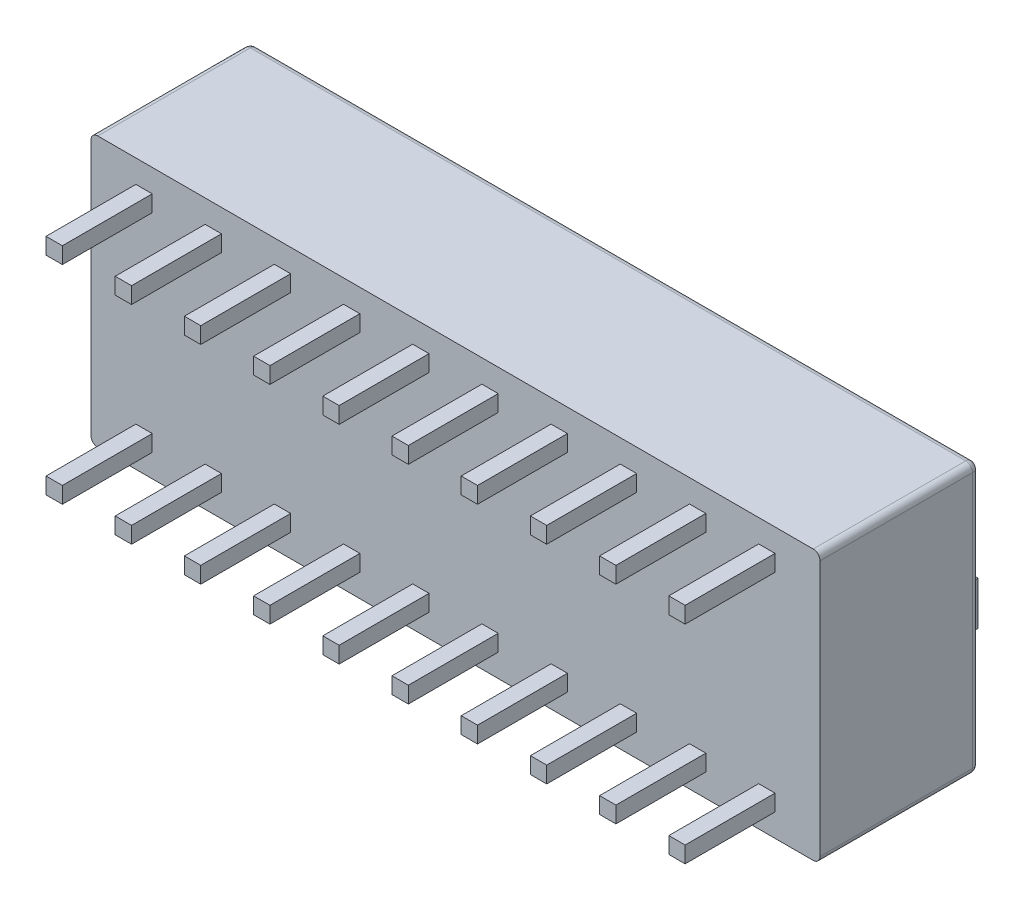
SolidWorks part; units mm, degrees
ref_plane "Ön Düzlem" through (0, 0, 0) normal (0, 0, 1) x (1, 0, 0)
ref_plane "Üst Düzlem" through (0, 0, 0) normal (0, 1, 0) x (1, 0, 0)
ref_plane "Sağ Düzlem" through (0, 0, 0) normal (1, 0, 0) x (0, 0, -1)
sketch "Çizim1" plane through (0, 0, 0) normal (0, 0, 1) x (1, 0, 0)
  line L1 (-13.38, 4.95) -> (13.38, 4.95)
  line L2 (-13.38, 4.95) -> (-13.38, -4.95)
  line L3 (-13.38, -4.95) -> (13.38, -4.95)
  line L4 (13.38, 4.95) -> (13.38, -4.95)
  line L5 (-13.38, 4.95) -> (13.38, -4.95) construction
  line L6 (-13.38, -4.95) -> (13.38, 4.95) construction
  point P0 (0, 0)
extrude "Yükseklik-Ekstrüzyon1" add sketch "Çizim1" along normal blind 5.85
sketch "Çizim2" plane through (0, 0, 0) normal (0, 0, -1) x (-1, 0, 0)
  line L1 (-12.13, 1.6) -> (-10.73, 1.6)
  line L11 (-12.13, 1.6) -> (-12.13, -1.6)
  line L12 (-12.13, -1.6) -> (-10.73, -1.6)
  line L13 (-10.73, 1.6) -> (-10.73, -1.6)
  line L14 (-12.13, 1.6) -> (-10.73, -1.6) construction
  line L15 (-12.13, -1.6) -> (-10.73, 1.6) construction
  line L16 (-9.59, 1.6) -> (-8.19, 1.6)
  line L17 (-9.59, 1.6) -> (-9.59, -1.6)
  line L18 (-9.59, -1.6) -> (-8.19, -1.6)
  line L19 (-8.19, 1.6) -> (-8.19, -1.6)
  line L20 (-9.59, 1.6) -> (-8.19, -1.6) construction
  line L21 (-9.59, -1.6) -> (-8.19, 1.6) construction
  line L22 (-7.05, 1.6) -> (-5.65, 1.6)
  line L23 (-7.05, 1.6) -> (-7.05, -1.6)
  line L24 (-7.05, -1.6) -> (-5.65, -1.6)
  line L25 (-5.65, 1.6) -> (-5.65, -1.6)
  line L26 (-7.05, 1.6) -> (-5.65, -1.6) construction
  line L27 (-7.05, -1.6) -> (-5.65, 1.6) construction
  line L28 (-4.51, 1.6) -> (-3.11, 1.6)
  line L29 (-4.51, 1.6) -> (-4.51, -1.6)
  line L30 (-4.51, -1.6) -> (-3.11, -1.6)
  line L31 (-3.11, 1.6) -> (-3.11, -1.6)
  line L32 (-4.51, 1.6) -> (-3.11, -1.6) construction
  line L33 (-4.51, -1.6) -> (-3.11, 1.6) construction
  line L34 (-1.97, 1.6) -> (-0.57, 1.6)
  line L35 (-1.97, 1.6) -> (-1.97, -1.6)
  line L36 (-1.97, -1.6) -> (-0.57, -1.6)
  line L37 (-0.57, 1.6) -> (-0.57, -1.6)
  line L38 (-1.97, 1.6) -> (-0.57, -1.6) construction
  line L39 (-1.97, -1.6) -> (-0.57, 1.6) construction
  line L40 (0.57, 1.6) -> (1.97, 1.6)
  line L41 (0.57, 1.6) -> (0.57, -1.6)
  line L42 (0.57, -1.6) -> (1.97, -1.6)
  line L43 (1.97, 1.6) -> (1.97, -1.6)
  line L44 (0.57, 1.6) -> (1.97, -1.6) construction
  line L45 (0.57, -1.6) -> (1.97, 1.6) construction
  line L46 (3.11, 1.6) -> (4.51, 1.6)
  line L47 (3.11, 1.6) -> (3.11, -1.6)
  line L48 (3.11, -1.6) -> (4.51, -1.6)
  line L49 (4.51, 1.6) -> (4.51, -1.6)
  line L50 (3.11, 1.6) -> (4.51, -1.6) construction
  line L51 (3.11, -1.6) -> (4.51, 1.6) construction
  line L52 (5.65, 1.6) -> (7.05, 1.6)
  line L53 (5.65, 1.6) -> (5.65, -1.6)
  line L54 (5.65, -1.6) -> (7.05, -1.6)
  line L55 (7.05, 1.6) -> (7.05, -1.6)
  line L56 (5.65, 1.6) -> (7.05, -1.6) construction
  line L57 (5.65, -1.6) -> (7.05, 1.6) construction
  line L58 (8.19, 1.6) -> (9.59, 1.6)
  line L59 (8.19, 1.6) -> (8.19, -1.6)
  line L60 (8.19, -1.6) -> (9.59, -1.6)
  line L61 (9.59, 1.6) -> (9.59, -1.6)
  line L62 (8.19, 1.6) -> (9.59, -1.6) construction
  line L63 (8.19, -1.6) -> (9.59, 1.6) construction
  line L64 (10.73, 1.6) -> (12.13, 1.6)
  line L65 (10.73, 1.6) -> (10.73, -1.6)
  line L66 (10.73, -1.6) -> (12.13, -1.6)
  line L67 (12.13, 1.6) -> (12.13, -1.6)
  line L68 (10.73, 1.6) -> (12.13, -1.6) construction
  line L69 (10.73, -1.6) -> (12.13, 1.6) construction
extrude "Kes-Ekstrüzyon1" cut sketch "Çizim2" against normal blind 1
sketch "Çizim3" plane through (0, 0, 1) normal (0, 0, -1) x (-1, 0, 0)
  line L0 (-10.73, -1.6) -> (-10.73, 1.6) construction
  line L1 (-12.13, -1.6) -> (-10.73, -1.6)
  line L2 (-12.13, -1.6) -> (-12.13, 0)
  line L3 (-12.13, 0) -> (-10.73, 0)
  line L4 (-10.73, -1.6) -> (-10.73, 0)
  line L5 (-9.59, 1.6) -> (-9.59, -1.6) construction
  line L6 (-9.59, 0) -> (-8.19, 0)
  line L7 (-9.59, 0) -> (-9.59, -1.6)
  line L8 (-9.59, -1.6) -> (-8.19, -1.6)
  line L9 (-8.19, 0) -> (-8.19, -1.6)
  line L10 (-7.05, -1.6) -> (-5.65, -1.6) construction
  line L11 (-7.05, -1.6) -> (-5.65, -1.6)
  line L12 (-7.05, -1.6) -> (-7.05, 0)
  line L13 (-7.05, 0) -> (-5.65, 0)
  line L14 (-5.65, -1.6) -> (-5.65, 0)
  line L15 (-7.05, -1.6) -> (-5.65, -1.6) construction
  line L16 (-5.65, -1.6) -> (-5.65, 1.6) construction
  line L17 (-4.51, 1.6) -> (-4.51, -1.6) construction
  line L18 (-4.51, 0) -> (-3.11, 0)
  line L19 (-4.51, 0) -> (-4.51, -1.6)
  line L20 (-4.51, -1.6) -> (-3.11, -1.6)
  line L21 (-3.11, 0) -> (-3.11, -1.6)
  line L22 (-0.57, -1.6) -> (-0.57, 1.6) construction
  line L23 (-1.97, -1.6) -> (-0.57, -1.6)
  line L24 (-1.97, -1.6) -> (-1.97, 0)
  line L25 (-1.97, 0) -> (-0.57, 0)
  line L26 (-0.57, -1.6) -> (-0.57, 0)
  line L27 (0.57, 1.6) -> (0.57, -1.6) construction
  line L28 (0.57, 0) -> (1.97, 0)
  line L29 (0.57, 0) -> (0.57, -1.6)
  line L30 (0.57, -1.6) -> (1.97, -1.6)
  line L31 (1.97, 0) -> (1.97, -1.6)
  line L32 (4.51, -1.6) -> (4.51, 1.6) construction
  line L33 (3.11, -1.6) -> (4.51, -1.6)
  line L34 (3.11, -1.6) -> (3.11, 0)
  line L35 (3.11, 0) -> (4.51, 0)
  line L36 (4.51, -1.6) -> (4.51, 0)
  line L37 (5.65, 1.6) -> (5.65, -1.6) construction
  line L38 (5.65, 0) -> (7.05, 0)
  line L39 (5.65, 0) -> (5.65, -1.6)
  line L40 (5.65, -1.6) -> (7.05, -1.6)
  line L41 (7.05, 0) -> (7.05, -1.6)
  line L42 (9.59, -1.6) -> (9.59, 1.6) construction
  line L43 (8.19, -1.6) -> (9.59, -1.6)
  line L44 (8.19, -1.6) -> (8.19, 0)
  line L45 (8.19, 0) -> (9.59, 0)
  line L46 (9.59, -1.6) -> (9.59, 0)
  line L47 (10.73, 1.6) -> (10.73, -1.6) construction
  line L48 (10.73, 0) -> (12.13, 0)
  line L49 (10.73, 0) -> (10.73, -1.6)
  line L50 (10.73, -1.6) -> (12.13, -1.6)
  line L51 (12.13, 0) -> (12.13, -1.6)
extrude "Yükseklik-Ekstrüzyon2" add sketch "Çizim3" along normal blind 2.2 separate body
sketch "Çizim4" plane through (0, 0, 1) normal (0, 0, -1) x (-1, 0, 0)
  line L0 (-10.73, -1.6) -> (-10.73, 1.6) construction
  line L1 (-12.13, 1.6) -> (-10.73, 1.6)
  line L2 (-12.13, 1.6) -> (-12.13, 0)
  line L3 (-12.13, 0) -> (-10.73, 0)
  line L4 (-10.73, 1.6) -> (-10.73, 0)
  line L5 (-5.65, -1.6) -> (-5.65, 1.6) construction
  line L6 (-9.59, 0) -> (-8.19, 0)
  line L7 (-9.59, 0) -> (-9.59, 1.6)
  line L8 (-9.59, 1.6) -> (-8.19, 1.6)
  line L9 (-8.19, 0) -> (-8.19, 1.6)
  line L10 (-7.05, 1.6) -> (-5.65, 1.6)
  line L11 (-7.05, 1.6) -> (-7.05, 0)
  line L12 (-7.05, 0) -> (-5.65, 0)
  line L13 (-5.65, 1.6) -> (-5.65, 0)
  line L14 (-0.57, -1.6) -> (-0.57, 1.6) construction
  line L15 (-4.51, 0) -> (-3.11, 0)
  line L16 (-4.51, 0) -> (-4.51, 1.6)
  line L17 (-4.51, 1.6) -> (-3.11, 1.6)
  line L18 (-3.11, 0) -> (-3.11, 1.6)
  line L19 (-1.97, 1.6) -> (-0.57, 1.6)
  line L20 (-1.97, 1.6) -> (-1.97, 0)
  line L21 (-1.97, 0) -> (-0.57, 0)
  line L22 (-0.57, 1.6) -> (-0.57, 0)
  line L23 (0.57, 1.6) -> (0.57, -1.6) construction
  line L24 (0.57, 0) -> (1.97, 0)
  line L25 (0.57, 0) -> (0.57, 1.6)
  line L26 (0.57, 1.6) -> (1.97, 1.6)
  line L27 (1.97, 0) -> (1.97, 1.6)
  line L28 (5.65, 1.6) -> (5.65, -1.6) construction
  line L29 (3.11, 1.6) -> (4.51, 1.6)
  line L30 (3.11, 1.6) -> (3.11, 0)
  line L31 (3.11, 0) -> (4.51, 0)
  line L32 (4.51, 1.6) -> (4.51, 0)
  line L33 (5.65, 0) -> (7.05, 0)
  line L34 (5.65, 0) -> (5.65, 1.6)
  line L35 (5.65, 1.6) -> (7.05, 1.6)
  line L36 (7.05, 0) -> (7.05, 1.6)
  line L37 (10.73, 1.6) -> (10.73, -1.6) construction
  line L38 (8.19, 1.6) -> (9.59, 1.6)
  line L39 (8.19, 1.6) -> (8.19, 0)
  line L40 (8.19, 0) -> (9.59, 0)
  line L41 (9.59, 1.6) -> (9.59, 0)
  line L42 (10.73, 0) -> (12.13, 0)
  line L43 (10.73, 0) -> (10.73, 1.6)
  line L44 (10.73, 1.6) -> (12.13, 1.6)
  line L45 (12.13, 0) -> (12.13, 1.6)
extrude "Yükseklik-Ekstrüzyon3" add sketch "Çizim4" along normal blind 0.9 separate body
fillet "Radyus1" radius 0.25 8 edges at (13.38, -4.95, 2.925) (13.38, 4.95, 2.925) (13.38, 0, 0) (-13.38, -4.95, 2.925) (-13.38, 4.95, 2.925) (0, -4.95, 0) (-13.38, 0, 0) (0, 4.95, 0)
sketch "Çizim5" plane through (0, 0, 5.85) normal (0, 0, 1) x (1, 0, 0)
  line L21 (11.73, -4.11) -> (11.13, -4.11)
  line L22 (11.73, -4.11) -> (11.73, -3.51)
  line L23 (11.73, -3.51) -> (11.13, -3.51)
  line L24 (11.13, -4.11) -> (11.13, -3.51)
  line L25 (11.73, -4.11) -> (11.13, -3.51) construction
  line L26 (11.73, -3.51) -> (11.13, -4.11) construction
  line L27 (9.19, -4.11) -> (8.59, -4.11)
  line L28 (9.19, -4.11) -> (9.19, -3.51)
  line L29 (9.19, -3.51) -> (8.59, -3.51)
  line L30 (8.59, -4.11) -> (8.59, -3.51)
  line L31 (9.19, -4.11) -> (8.59, -3.51) construction
  line L32 (9.19, -3.51) -> (8.59, -4.11) construction
  line L33 (6.65, -4.11) -> (6.05, -4.11)
  line L34 (6.65, -4.11) -> (6.65, -3.51)
  line L35 (6.65, -3.51) -> (6.05, -3.51)
  line L36 (6.05, -4.11) -> (6.05, -3.51)
  line L37 (6.65, -4.11) -> (6.05, -3.51) construction
  line L38 (6.65, -3.51) -> (6.05, -4.11) construction
  line L39 (4.11, -4.11) -> (3.51, -4.11)
  line L40 (4.11, -4.11) -> (4.11, -3.51)
  line L41 (4.11, -3.51) -> (3.51, -3.51)
  line L42 (3.51, -4.11) -> (3.51, -3.51)
  line L43 (4.11, -4.11) -> (3.51, -3.51) construction
  line L44 (4.11, -3.51) -> (3.51, -4.11) construction
  line L45 (1.57, -4.11) -> (0.97, -4.11)
  line L46 (1.57, -4.11) -> (1.57, -3.51)
  line L47 (1.57, -3.51) -> (0.97, -3.51)
  line L48 (0.97, -4.11) -> (0.97, -3.51)
  line L49 (1.57, -4.11) -> (0.97, -3.51) construction
  line L50 (1.57, -3.51) -> (0.97, -4.11) construction
  line L51 (-0.97, -4.11) -> (-1.57, -4.11)
  line L52 (-0.97, -4.11) -> (-0.97, -3.51)
  line L53 (-0.97, -3.51) -> (-1.57, -3.51)
  line L54 (-1.57, -4.11) -> (-1.57, -3.51)
  line L55 (-0.97, -4.11) -> (-1.57, -3.51) construction
  line L56 (-0.97, -3.51) -> (-1.57, -4.11) construction
  line L57 (-3.51, -4.11) -> (-4.11, -4.11)
  line L58 (-3.51, -4.11) -> (-3.51, -3.51)
  line L59 (-3.51, -3.51) -> (-4.11, -3.51)
  line L60 (-4.11, -4.11) -> (-4.11, -3.51)
  line L61 (-3.51, -4.11) -> (-4.11, -3.51) construction
  line L62 (-3.51, -3.51) -> (-4.11, -4.11) construction
  line L63 (-6.05, -4.11) -> (-6.65, -4.11)
  line L64 (-6.05, -4.11) -> (-6.05, -3.51)
  line L65 (-6.05, -3.51) -> (-6.65, -3.51)
  line L66 (-6.65, -4.11) -> (-6.65, -3.51)
  line L67 (-6.05, -4.11) -> (-6.65, -3.51) construction
  line L68 (-6.05, -3.51) -> (-6.65, -4.11) construction
  line L69 (-8.59, -4.11) -> (-9.19, -4.11)
  line L70 (-8.59, -4.11) -> (-8.59, -3.51)
  line L71 (-8.59, -3.51) -> (-9.19, -3.51)
  line L72 (-9.19, -4.11) -> (-9.19, -3.51)
  line L73 (-8.59, -4.11) -> (-9.19, -3.51) construction
  line L74 (-8.59, -3.51) -> (-9.19, -4.11) construction
  line L75 (-11.13, -4.11) -> (-11.73, -4.11)
  line L76 (-11.13, -4.11) -> (-11.13, -3.51)
  line L77 (-11.13, -3.51) -> (-11.73, -3.51)
  line L78 (-11.73, -4.11) -> (-11.73, -3.51)
  line L79 (-11.13, -4.11) -> (-11.73, -3.51) construction
  line L80 (-11.13, -3.51) -> (-11.73, -4.11) construction
  line L81 (-11.13, 3.51) -> (-11.73, 3.51)
  line L82 (-11.13, 3.51) -> (-11.13, 4.11)
  line L83 (-11.13, 4.11) -> (-11.73, 4.11)
  line L84 (-11.73, 3.51) -> (-11.73, 4.11)
  line L85 (-11.13, 3.51) -> (-11.73, 4.11) construction
  line L86 (-11.13, 4.11) -> (-11.73, 3.51) construction
  line L87 (-8.59, 3.51) -> (-9.19, 3.51)
  line L88 (-8.59, 3.51) -> (-8.59, 4.11)
  line L89 (-8.59, 4.11) -> (-9.19, 4.11)
  line L90 (-9.19, 3.51) -> (-9.19, 4.11)
  line L91 (-8.59, 3.51) -> (-9.19, 4.11) construction
  line L92 (-8.59, 4.11) -> (-9.19, 3.51) construction
  line L93 (-6.05, 3.51) -> (-6.65, 3.51)
  line L94 (-6.05, 3.51) -> (-6.05, 4.11)
  line L95 (-6.05, 4.11) -> (-6.65, 4.11)
  line L96 (-6.65, 3.51) -> (-6.65, 4.11)
  line L97 (-6.05, 3.51) -> (-6.65, 4.11) construction
  line L98 (-6.05, 4.11) -> (-6.65, 3.51) construction
  line L99 (-3.51, 3.51) -> (-4.11, 3.51)
  line L100 (-3.51, 3.51) -> (-3.51, 4.11)
  line L101 (-3.51, 4.11) -> (-4.11, 4.11)
  line L102 (-4.11, 3.51) -> (-4.11, 4.11)
  line L103 (-3.51, 3.51) -> (-4.11, 4.11) construction
  line L104 (-3.51, 4.11) -> (-4.11, 3.51) construction
  line L105 (-0.97, 3.51) -> (-1.57, 3.51)
  line L106 (-0.97, 3.51) -> (-0.97, 4.11)
  line L107 (-0.97, 4.11) -> (-1.57, 4.11)
  line L108 (-1.57, 3.51) -> (-1.57, 4.11)
  line L109 (-0.97, 3.51) -> (-1.57, 4.11) construction
  line L110 (-0.97, 4.11) -> (-1.57, 3.51) construction
  line L111 (1.57, 3.51) -> (0.97, 3.51)
  line L112 (1.57, 3.51) -> (1.57, 4.11)
  line L113 (1.57, 4.11) -> (0.97, 4.11)
  line L114 (0.97, 3.51) -> (0.97, 4.11)
  line L115 (1.57, 3.51) -> (0.97, 4.11) construction
  line L116 (1.57, 4.11) -> (0.97, 3.51) construction
  line L117 (4.11, 3.51) -> (3.51, 3.51)
  line L118 (4.11, 3.51) -> (4.11, 4.11)
  line L119 (4.11, 4.11) -> (3.51, 4.11)
  line L120 (3.51, 3.51) -> (3.51, 4.11)
  line L121 (4.11, 3.51) -> (3.51, 4.11) construction
  line L122 (4.11, 4.11) -> (3.51, 3.51) construction
  line L123 (6.65, 3.51) -> (6.05, 3.51)
  line L124 (6.65, 3.51) -> (6.65, 4.11)
  line L125 (6.65, 4.11) -> (6.05, 4.11)
  line L126 (6.05, 3.51) -> (6.05, 4.11)
  line L127 (6.65, 3.51) -> (6.05, 4.11) construction
  line L128 (6.65, 4.11) -> (6.05, 3.51) construction
  line L129 (9.19, 3.51) -> (8.59, 3.51)
  line L130 (9.19, 3.51) -> (9.19, 4.11)
  line L131 (9.19, 4.11) -> (8.59, 4.11)
  line L132 (8.59, 3.51) -> (8.59, 4.11)
  line L133 (9.19, 3.51) -> (8.59, 4.11) construction
  line L134 (9.19, 4.11) -> (8.59, 3.51) construction
  line L135 (11.73, 3.51) -> (11.13, 3.51)
  line L136 (11.73, 3.51) -> (11.73, 4.11)
  line L137 (11.73, 4.11) -> (11.13, 4.11)
  line L138 (11.13, 3.51) -> (11.13, 4.11)
  line L139 (11.73, 3.51) -> (11.13, 4.11) construction
  line L140 (11.73, 4.11) -> (11.13, 3.51) construction
  point P121 (0.97, -3.81)
extrude "Yükseklik-Ekstrüzyon4" add sketch "Çizim5" along normal blind 3.3
